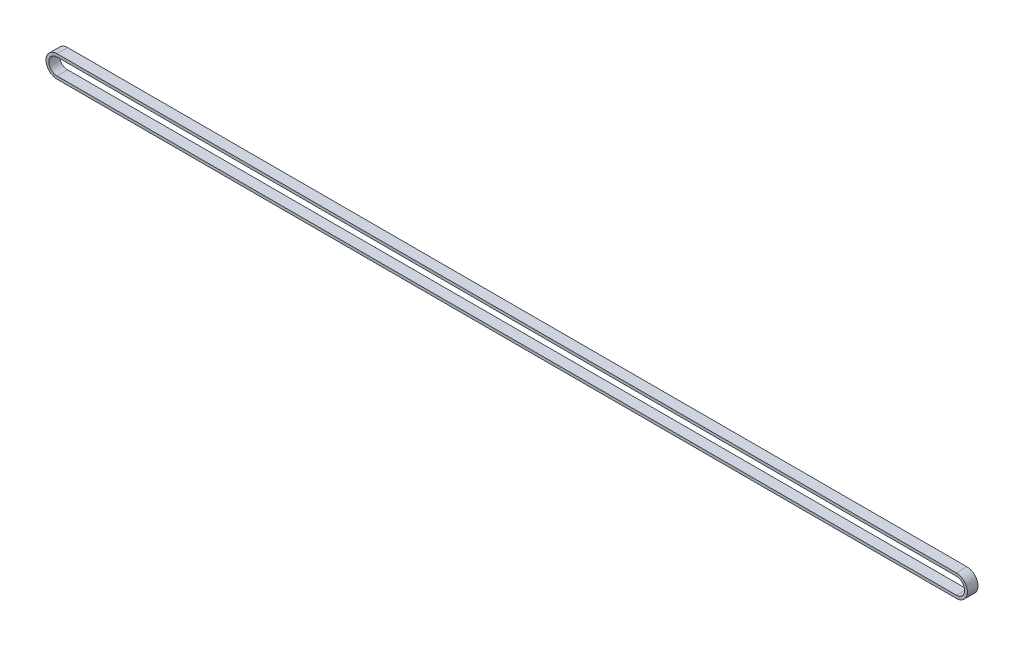
SolidWorks part; units mm, degrees
ref_plane "Plano frontal" through (0, 0, 0) normal (0, 0, 1) x (1, 0, 0)
ref_plane "Plano superior" through (0, 0, 0) normal (0, 1, 0) x (1, 0, 0)
ref_plane "Plano direito" through (0, 0, 0) normal (1, 0, 0) x (0, 0, -1)
ref_plane "Plano1" through (0, 0, 6.25) normal (0, 0, 1) x (1, 0, 0)
sketch "Esboço1" plane through (0, 0, 6.25) normal (0, 0, 1) x (1, 0, 0)
  line L0 (528.475, 6.5) -> (0, 6.5)
  line L1 (0, -6.5) -> (528.475, -6.5)
  line L2 (0, 4.848) -> (528.475, 4.848)
  line L3 (528.475, -4.848) -> (0, -4.848)
  arc A0 (0, 6.5) -> (0, -6.5) centre (0, 0) ccw
  arc A1 (528.475, -6.5) -> (528.475, 6.5) centre (528.475, 0) ccw
  arc A2 (0, -4.848) -> (0, 4.848) centre (0, 0) cw
  arc A3 (528.475, 4.848) -> (528.475, -4.848) centre (528.475, 0) cw
extrude "Ressalto-extrusão1" add sketch "Esboço1" against normal blind 6.25
